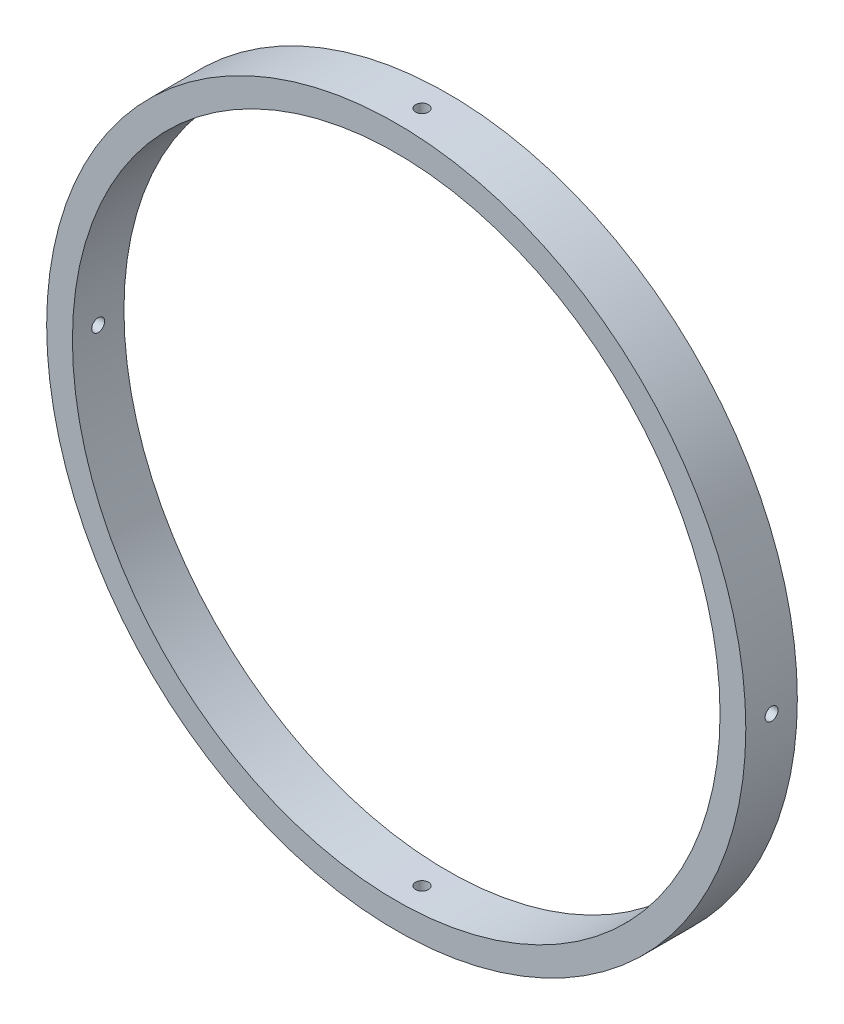
SolidWorks part; units mm, degrees
ref_plane "Front Plane" through (0, 0, 0) normal (0, 0, 1) x (1, 0, 0)
ref_plane "Top Plane" through (0, 0, 0) normal (0, 1, 0) x (1, 0, 0)
ref_plane "Right Plane" through (0, 0, 0) normal (1, 0, 0) x (0, 0, -1)
sketch "Sketch3" plane through (0, 0, 0) normal (0, 0, 1) x (1, 0, 0)
  circle A0 centre (0, 0) radius 39.9034
  circle A1 centre (0, 0) radius 43.0784
  dimension "D1" = 79.8068
  dimension "D2" = 3.175
extrude "Boss-Extrude1" add sketch "Sketch3" along normal mid plane 6.35
sketch "Sketch4" plane through (0, 0, 0) normal (0, 1, 0) x (1, 0, 0)
  circle A0 centre (0, 0) radius 0.7937
  dimension "D1" = 1.5875
extrude "Cut-Extrude1" cut sketch "Sketch4" against normal through all
pattern_circular "CirPattern1" count 4 over 360 about axis through (0, 0, 3.175) along (0, 0, -1) of "Cut-Extrude1"
equation "\"AIRFRAME_OD\"= 3.142in"
equation "\"AIRFRAME_ID\"= 3.00in"
equation "\"FLAT_T\"= 0.125in"
equation "\"NOSE_EXP_L\"= 3.5in"
equation "\"NOSE_SHOULDER_L\"= 1.5in"
equation "\"MAIN_L\"= 30in"
equation "\"RECO_COUP_L\"= 6in"
equation "\"RECO_SWITCH_L\"= 1.5in"
equation "\"DROGUE_L\"= 14in"
equation "\"ATS_FORE_COUP_L\"= 4in"
equation "\"ATS_AFT_COUP_L\"= 2.5in"
equation "\"LOWER_L\"= 16in"
equation "\"FIN_N\"= 4"
equation "\"CR_AFT_X\"= 0.5in"
equation "\"CR_FORE_X\"= 6in"
equation "\"COUPLER_OD\"= 2.998in"
equation "\"COUPLER_ID\"= 2.875in"
equation "\"RECO_ROD_X\"= 1.5in"
equation "\"ATS_ROD_X\"= 2in"
equation "\"FIN_ROOT\"= 5in"
equation "\"FIN_X\"= 0.75in"
equation "\"MOTOR_OD\"= 2.25in"
equation "\"MOTOR_ID\"= 2.126in"
equation "\"MOTOR_L\"= 8in"
equation "\"MOTOR_LOWER_X\"= 0.5in"
equation "\"D1@Sketch3\"=\"AIRFRAME_OD\""
